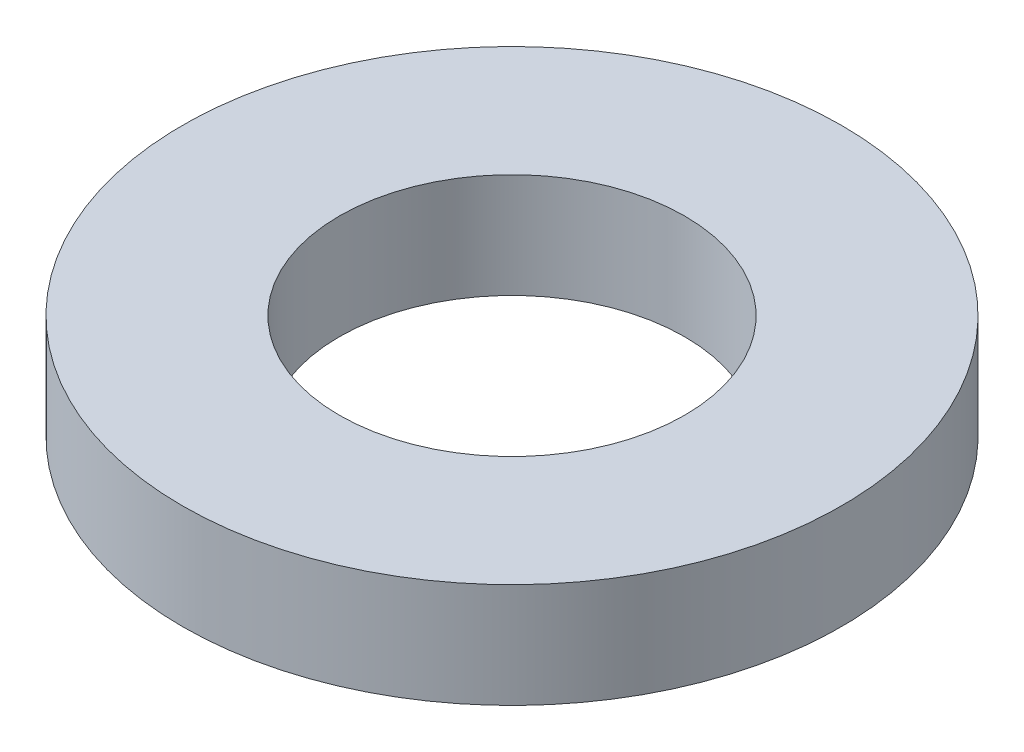
SolidWorks part; units mm, degrees
ref_plane "Front Plane" through (0, 0, 0) normal (0, 0, 1) x (1, 0, 0)
ref_plane "Top Plane" through (0, 0, 0) normal (0, 1, 0) x (1, 0, 0)
ref_plane "Right Plane" through (0, 0, 0) normal (1, 0, 0) x (0, 0, -1)
sketch "Sketch1" plane through (0, 0, 0) normal (0, 1, 0) x (1, 0, 0)
  circle A0 centre (0, 0) radius 31.5
  circle A1 centre (0, 0) radius 16.5
  dimension "D1" = 63
  dimension "D2" = 33
extrude "Boss-Extrude1" add sketch "Sketch1" along normal blind 10
